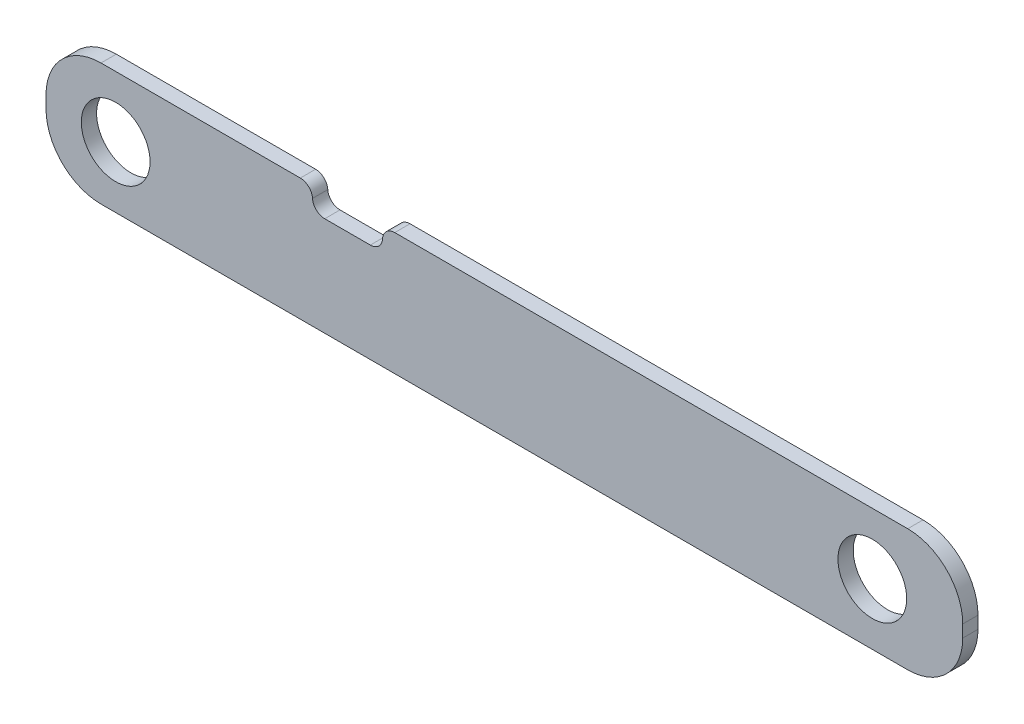
SolidWorks part; units mm, degrees
ref_plane "Front Plane" through (0, 0, 0) normal (0, 0, 1) x (1, 0, 0)
ref_plane "Top Plane" through (0, 0, 0) normal (0, 1, 0) x (1, 0, 0)
ref_plane "Right Plane" through (0, 0, 0) normal (1, 0, 0) x (0, 0, -1)
sketch "Sketch2" plane through (0, 0, 0) normal (0, 0, 1) x (1, 0, 0)
  line L1 (-237.2264, 105.434) -> (143.7736, 105.434)
  line L2 (-237.2264, 105.434) -> (-237.2264, 54.634)
  line L3 (-237.2264, 54.634) -> (143.7736, 54.634)
  line L4 (143.7736, 105.434) -> (143.7736, 54.634)
  dimension "D1" = 381
  dimension "D2" = 50.8
extrude "Boss-Extrude1" add sketch "Sketch2" along normal blind 6.35
sketch "Sketch3" plane through (0, 0, 6.35) normal (0, 0, 1) x (1, 0, 0)
  line L0 (-126.4438, 105.434) -> (-126.4438, 95.8582)
  line L1 (143.7736, 105.434) -> (-237.2264, 105.434) construction
  line L2 (-126.4438, 95.8582) -> (-97.3591, 95.8582)
  line L3 (-97.3591, 95.8582) -> (-97.3591, 105.434)
  line L4 (-126.4438, 105.434) -> (-97.3591, 105.434)
  circle A0 centre (-208.2707, 80.034) radius 14.2875
  circle A1 centre (106.1951, 80.034) radius 14.2875
  dimension "D1" = 28.575
  dimension "D2" = 28.575
extrude "Cut-Extrude1" cut sketch "Sketch3" against normal blind 6.35
fillet "Fillet4" radius 22.86 1 edges at (143.7736, 105.434, 3.175)
fillet "Fillet5" radius 22.86 1 edges at (143.7736, 54.634, 3.175)
fillet "Fillet6" radius 22.86 1 edges at (-237.2264, 54.634, 3.175)
fillet "Fillet7" radius 22.86 1 edges at (-237.2264, 105.434, 3.175)
fillet "Fillet12" radius 5.08 1 edges at (-126.4438, 105.434, 3.175)
fillet "Fillet13" radius 5.08 1 edges at (-97.3591, 105.434, 3.175)
fillet "Fillet14" radius 5.08 1 edges at (-126.4438, 95.8582, 3.175)
fillet "Fillet15" radius 5.08 1 edges at (-97.3591, 95.8582, 3.175)
